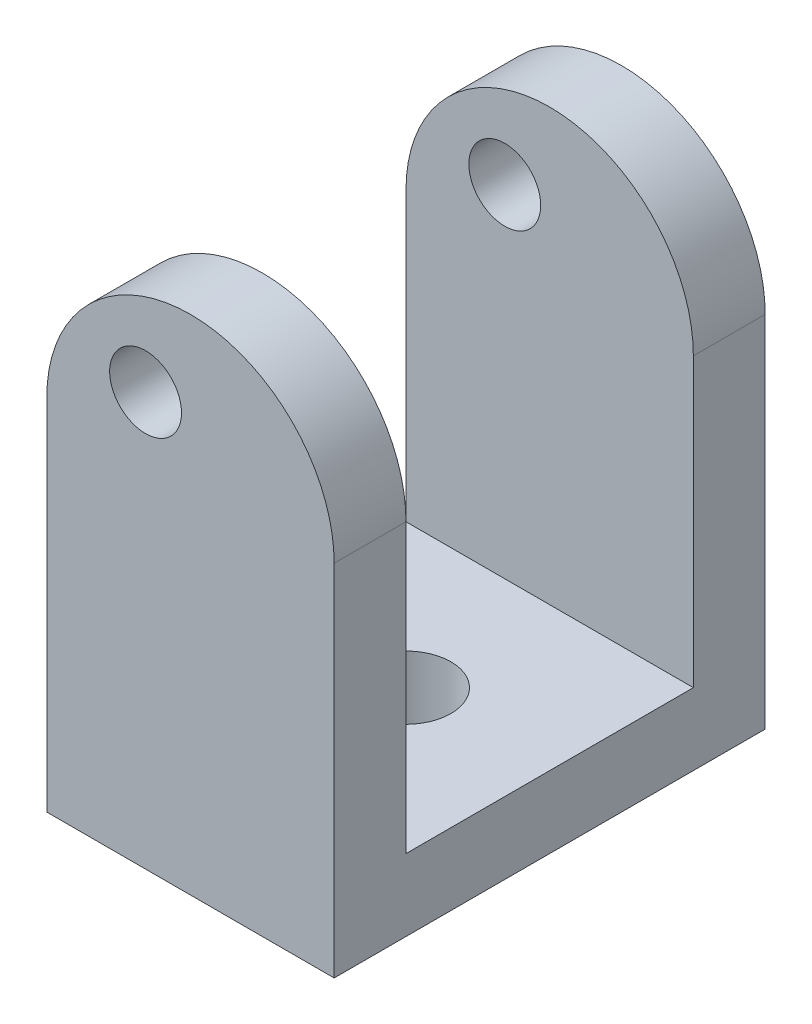
SolidWorks part; units mm, degrees
material "PPE"
ref_plane "Front Plane" through (0, 0, 0) normal (0, 0, 1) x (1, 0, 0)
ref_plane "Top Plane" through (0, 0, 0) normal (0, 1, 0) x (1, 0, 0)
ref_plane "Right Plane" through (0, 0, 0) normal (1, 0, 0) x (0, 0, -1)
sketch "Sketch1" plane through (0, 0, 0) normal (0, 1, 0) x (1, 0, 0)
  line L1 (-28.575, -19.05) -> (28.575, -19.05)
  line L2 (-28.575, -19.05) -> (-28.575, 19.05)
  line L3 (-28.575, 19.05) -> (28.575, 19.05)
  line L4 (28.575, -19.05) -> (28.575, 19.05)
  line L5 (-28.575, -19.05) -> (28.575, 19.05) construction
  line L6 (-28.575, 19.05) -> (28.575, -19.05) construction
  point P0 (0, 0)
  dimension "D1" = 57.15
  dimension "D2" = 38.1
extrude "Boss-Extrude1" add sketch "Sketch1" along normal blind 50.8
sketch "Sketch4" plane through (-28.575, 0, 0) normal (-1, 0, 0) x (0, 0, 1)
  line L0 (-19.05, 50.8) -> (19.05, 50.8) construction
  line L1 (-12.7, 50.8) -> (12.7, 50.8)
  line L2 (-12.7, 50.8) -> (-12.7, 6.35)
  line L3 (-12.7, 6.35) -> (12.7, 6.35)
  line L4 (12.7, 50.8) -> (12.7, 6.35)
  line L5 (-19.05, 50.8) -> (-19.05, 0) construction
  line L6 (19.05, 50.8) -> (19.05, 0) construction
  line L7 (-19.05, 0) -> (19.05, 0) construction
  dimension "D1" = 6.35
  dimension "D2" = 6.35
  dimension "D3" = 6.35
extrude "Cut-Extrude2" cut sketch "Sketch4" against normal through all
sketch "Sketch2" plane through (0, 0, 19.05) normal (0, 0, 1) x (1, 0, 0)
  line L0 (28.575, 0) -> (28.575, 15.875)
  line L1 (28.575, 50.8) -> (28.575, 0) construction
  line L2 (-3.175, 31.75) -> (-3.175, 0)
  line L3 (-28.575, 31.75) -> (-28.575, 0)
  line L4 (-28.575, 0) -> (28.575, 0) construction
  line L6 (-15.875, 0) -> (-15.875, 50.8) construction
  line L7 (-28.575, 50.8) -> (28.575, 50.8) construction
  line L8 (-28.575, 50.8) -> (-28.575, 0) construction
  circle A1 centre (-19.8438, 36.5125) radius 3.175
  arc A5 (-3.175, 31.75) -> (-28.575, 31.75) centre (-15.875, 31.75) ccw
  point P11 (-28.575, 50.8)
  point P12 (-19.8438, 36.5125)
  dimension "D2" = 25.4
  dimension "D5" = 6.35
  dimension "D6" = 12.7
  dimension "D7" = 19.05
  dimension "D1" = 15.875
  dimension "D3" = 8.7312
  dimension "D4" = 36.5125
extrude "Cut-Extrude1" cut sketch "Sketch2" against normal through all
sketch "Sketch5" plane through (0, 0, 0) normal (0, -1, 0) x (1, 0, 0)
  line L0 (-3.175, 0) -> (-28.575, 0) construction
  line L1 (-28.575, -19.05) -> (-28.575, 19.05) construction
  line L6 (-3.175, -19.05) -> (-3.175, 19.05) construction
  circle A0 centre (-15.875, 0) radius 3.9688
  dimension "D1" = 7.9375
  dimension "D2" = 12.7
extrude "Cut-Extrude3" cut sketch "Sketch5" against normal through all
scale "Scale1" [suppressed]
